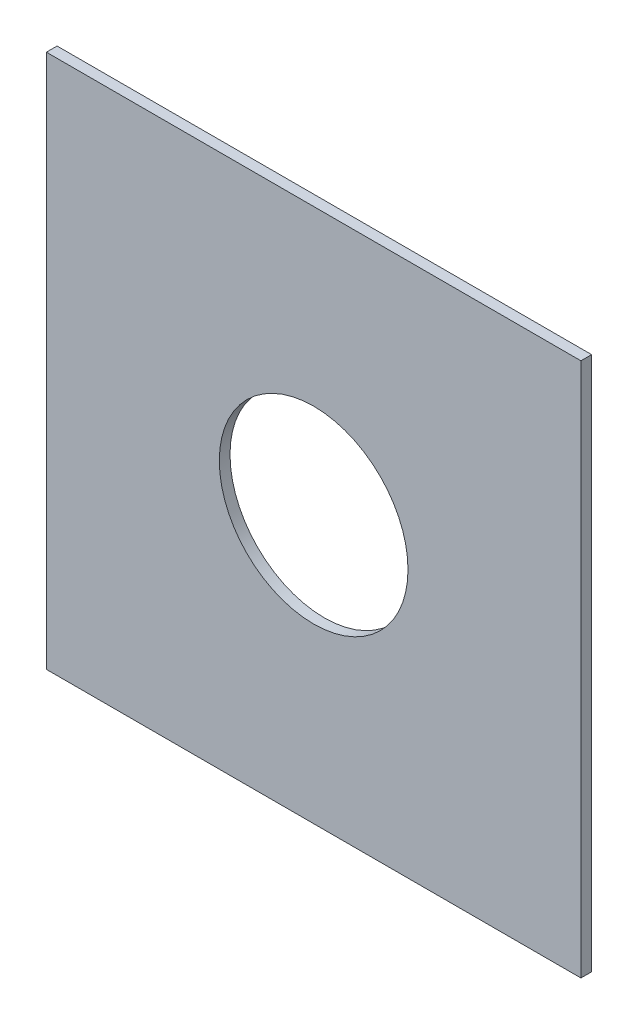
SolidWorks part; units mm, degrees
ref_plane "Front Plane" through (0, 0, 0) normal (0, 0, 1) x (1, 0, 0)
ref_plane "Top Plane" through (0, 0, 0) normal (0, 1, 0) x (1, 0, 0)
ref_plane "Right Plane" through (0, 0, 0) normal (1, 0, 0) x (0, 0, -1)
sketch "Sketch1" plane through (0, 0, 0) normal (0, 0, 1) x (1, 0, 0)
  line L0 (0, -55) -> (0, 55) construction
  line L1 (-250, -250) -> (250, -250)
  line L2 (-250, -250) -> (-250, 250)
  line L3 (-250, 250) -> (250, 250)
  line L4 (250, -250) -> (250, 250)
  line L5 (-250, -250) -> (250, 250) construction
  line L6 (-250, 250) -> (250, -250) construction
  circle A0 centre (0, 0) radius 88.25
  dimension "D1" = 250
  dimension "D3" = 176.5
  dimension "D2" = 250
extrude "Boss-Extrude1" add sketch "Sketch1" along normal blind 10
